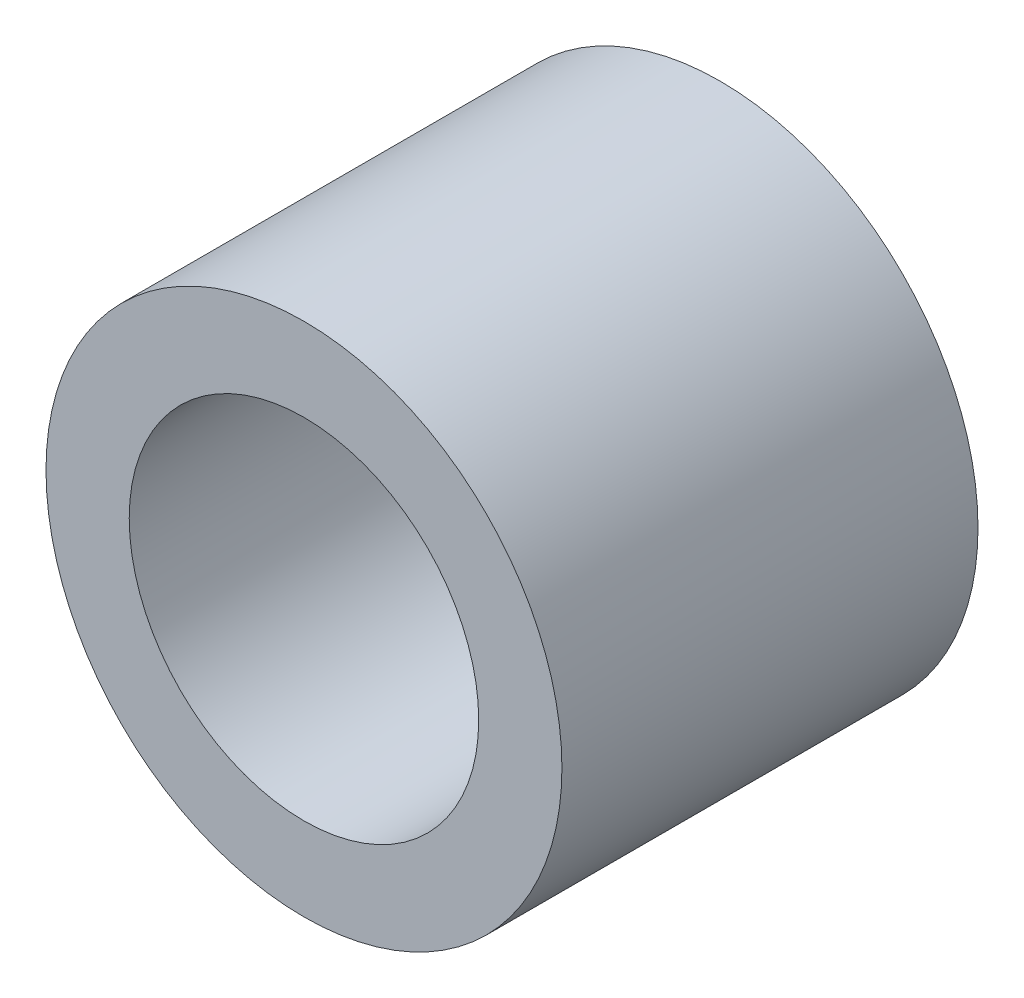
SolidWorks part; units mm, degrees
ref_plane "Front Plane" through (0, 0, 0) normal (0, 0, 1) x (1, 0, 0)
ref_plane "Top Plane" through (0, 0, 0) normal (0, 1, 0) x (1, 0, 0)
ref_plane "Right Plane" through (0, 0, 0) normal (1, 0, 0) x (0, 0, -1)
sketch "Sketch3" plane through (0, 0, 0) normal (0, 0, 1) x (1, 0, 0)
  circle A0 centre (0, 0) radius 2.1
  circle A1 centre (0, 0) radius 3.1
  dimension "D1" = 6.2
  dimension "D2" = 4.2
extrude "Boss-Extrude1" add sketch "Sketch3" along normal blind 5
